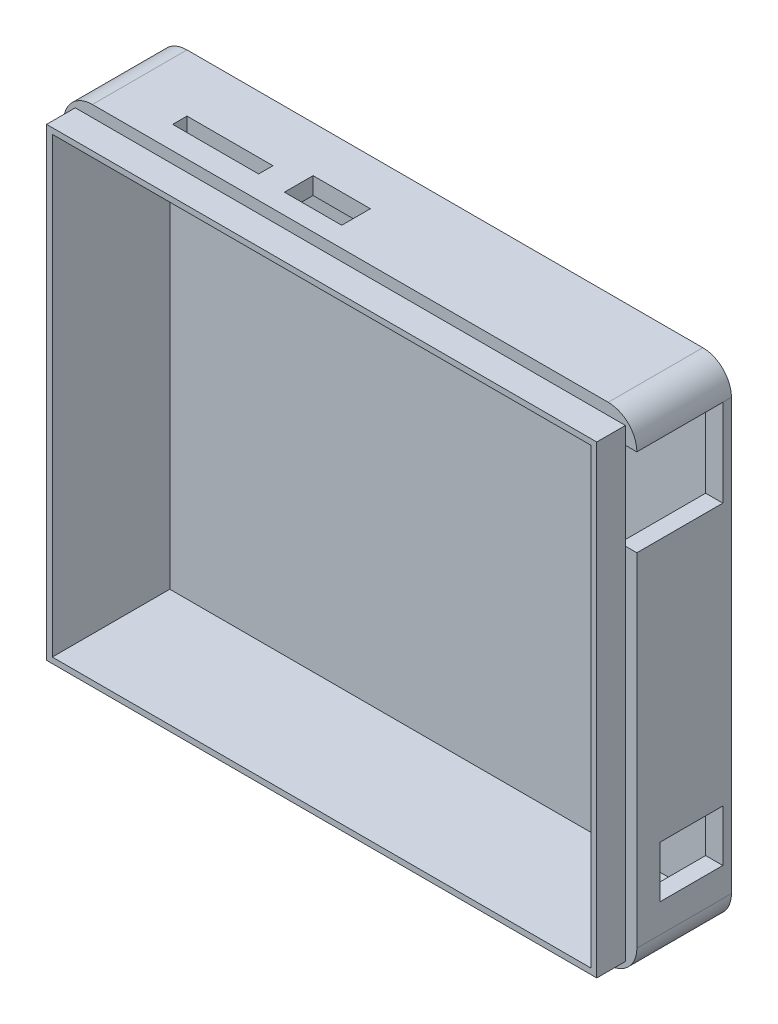
SolidWorks part; units mm, degrees
ref_plane "Front Plane" through (0, 0, 0) normal (0, 0, 1) x (1, 0, 0)
ref_plane "Top Plane" through (0, 0, 0) normal (0, 1, 0) x (1, 0, 0)
ref_plane "Right Plane" through (0, 0, 0) normal (1, 0, 0) x (0, 0, -1)
sketch "Sketch1" plane through (0, 0, 0) normal (0, 0, 1) x (1, 0, 0)
  line L1 (-50, 42.5) -> (50, 42.5)
  line L2 (-50, 42.5) -> (-50, -42.5)
  line L3 (-50, -42.5) -> (50, -42.5)
  line L4 (50, 42.5) -> (50, -42.5)
  line L5 (-50, 42.5) -> (50, -42.5) construction
  line L6 (-50, -42.5) -> (50, 42.5) construction
  point P0 (0, 0)
  dimension "D1" = 100
  dimension "D2" = 85
extrude "Boss-Extrude2" add sketch "Sketch1" along normal blind 20
sketch "Sketch3" plane through (0, 0, 20) normal (0, 0, 1) x (1, 0, 0)
  line L1 (-48, 40.5) -> (48, 40.5)
  line L2 (-48, 40.5) -> (-48, -40.5)
  line L3 (-48, -40.5) -> (48, -40.5)
  line L4 (48, 40.5) -> (48, -40.5)
  line L5 (-48, 40.5) -> (48, -40.5) construction
  line L6 (-48, -40.5) -> (48, 40.5) construction
  line L7 (-50, -42.5) -> (50, -42.5)
  line L8 (-50, -42.5) -> (-50, 42.5)
  line L9 (-50, 42.5) -> (50, 42.5)
  line L10 (50, -42.5) -> (50, 42.5)
  line L11 (-50, -42.5) -> (50, 42.5) construction
  line L12 (-50, 42.5) -> (50, -42.5) construction
  point P0 (0, 0)
  point P6 (0, 0)
  dimension "D1" = 96
  dimension "D2" = 81
extrude "Cut-Extrude1" cut sketch "Sketch3" against normal blind 5
sketch "Sketch4" plane through (0, 0, 20) normal (0, 0, 1) x (1, 0, 0)
  line L1 (-47, 39.5) -> (47, 39.5)
  line L2 (-47, 39.5) -> (-47, -39.5)
  line L3 (-47, -39.5) -> (47, -39.5)
  line L4 (47, 39.5) -> (47, -39.5)
  line L5 (-47, 39.5) -> (47, -39.5) construction
  line L6 (-47, -39.5) -> (47, 39.5) construction
  point P0 (0, 0)
  dimension "D1" = 94
  dimension "D2" = 79
extrude "Cut-Extrude2" cut sketch "Sketch4" against normal blind 19
sketch "Sketch9" plane through (0, 0, 0) normal (0, 0, -1) x (-1, 0, 0)
  line L1 (-50, 42.5) -> (50, 42.5)
  line L2 (-50, 42.5) -> (-50, -42.5)
  line L3 (-50, -42.5) -> (50, -42.5)
  line L4 (50, 42.5) -> (50, -42.5)
  line L5 (-50, 42.5) -> (50, -42.5) construction
  line L6 (-50, -42.5) -> (50, 42.5) construction
  point P0 (0, 0)
extrude "Boss-Extrude3" add sketch "Sketch9" along normal blind 1.5
sketch "Sketch10" plane through (0, 0, 1) normal (0, 0, 1) x (1, 0, 0)
  line L1 (-47, -39.5) -> (47, -39.5)
  line L2 (-47, -39.5) -> (-47, 39.5)
  line L3 (-47, 39.5) -> (47, 39.5)
  line L4 (47, -39.5) -> (47, 39.5)
  line L5 (-47, -39.5) -> (47, 39.5) construction
  line L6 (-47, 39.5) -> (47, -39.5) construction
  point P0 (0, 0)
extrude "Cut-Extrude5" cut sketch "Sketch10" against normal blind 1.5
sketch "Sketch11" plane through (50, 0, 0) normal (1, 0, 0) x (0, 0, -1)
  line L0 (-15, -42.5) -> (1.5, -42.5) construction
  line L1 (-11, -23.5) -> (0, -23.5)
  line L2 (-11, -23.5) -> (-11, -32.5)
  line L3 (-11, -32.5) -> (0, -32.5)
  line L4 (0, -23.5) -> (0, -32.5)
  line L5 (-11, -23.5) -> (0, -32.5) construction
  line L6 (-11, -32.5) -> (0, -23.5) construction
  line L7 (1.5, 42.5) -> (1.5, -42.5) construction
  point P0 (-5.5, -28)
  dimension "D1" = 11
  dimension "D2" = 9
  dimension "D3" = 10
  dimension "D4" = 1.5
extrude "Cut-Extrude7" cut sketch "Sketch11" against normal blind 50
sketch "Sketch12" plane through (50, 0, 0) normal (1, 0, 0) x (0, 0, -1)
  line L0 (-15, 42.5) -> (1.5, 42.5) construction
  line L1 (-15, 37.5) -> (0, 37.5)
  line L2 (-15, 37.5) -> (-15, 22.26)
  line L3 (-15, 22.26) -> (0, 22.26)
  line L4 (0, 37.5) -> (0, 22.26)
  line L5 (-15, 37.5) -> (0, 22.26) construction
  line L6 (-15, 22.26) -> (0, 37.5) construction
  line L7 (1.5, 42.5) -> (1.5, -42.5) construction
  point P0 (-7.5, 29.88)
  dimension "D1" = 15
  dimension "D2" = 15.24
  dimension "D3" = 5
  dimension "D4" = 1.5
extrude "Cut-Extrude8" cut sketch "Sketch12" against normal blind 50
sketch "Sketch13" plane through (0, 42.5, 0) normal (0, 1, 0) x (1, 0, 0)
  line L0 (-50, 1.5) -> (50, 1.5) construction
  line L1 (-35, -8.5) -> (-20, -8.5)
  line L2 (-35, -8.5) -> (-35, -11)
  line L3 (-35, -11) -> (-20, -11)
  line L4 (-20, -8.5) -> (-20, -11)
  line L5 (-35, -8.5) -> (-20, -11) construction
  line L6 (-35, -11) -> (-20, -8.5) construction
  line L7 (-50, -15) -> (-50, 1.5) construction
  point P0 (-27.5, -9.75)
  dimension "D1" = 15
  dimension "D2" = 2.5
  dimension "D3" = 10
  dimension "D4" = 15
extrude "Cut-Extrude9" cut sketch "Sketch13" against normal blind 50
sketch "Sketch14" plane through (0, 42.5, 0) normal (0, 1, 0) x (1, 0, 0)
  line L0 (50, -15) -> (50, 1.5) construction
  line L1 (-15, -6.5) -> (-5, -6.5)
  line L2 (-15, -6.5) -> (-15, -11.5)
  line L3 (-15, -11.5) -> (-5, -11.5)
  line L4 (-5, -6.5) -> (-5, -11.5)
  line L5 (-15, -6.5) -> (-5, -11.5) construction
  line L6 (-15, -11.5) -> (-5, -6.5) construction
  line L7 (-50, 1.5) -> (50, 1.5) construction
  point P0 (-10, -9)
  point P5 (-5, -9)
  dimension "D1" = 10
  dimension "D2" = 5
  dimension "D3" = 55
  dimension "D4" = 8
extrude "Cut-Extrude10" cut sketch "Sketch14" against normal blind 50
fillet "Fillet1" radius 5 4 edges at (-50, 42.5, 6.75) (-50, -42.5, 6.75) (50, 42.5, 6.75) (50, -42.5, 6.75)
